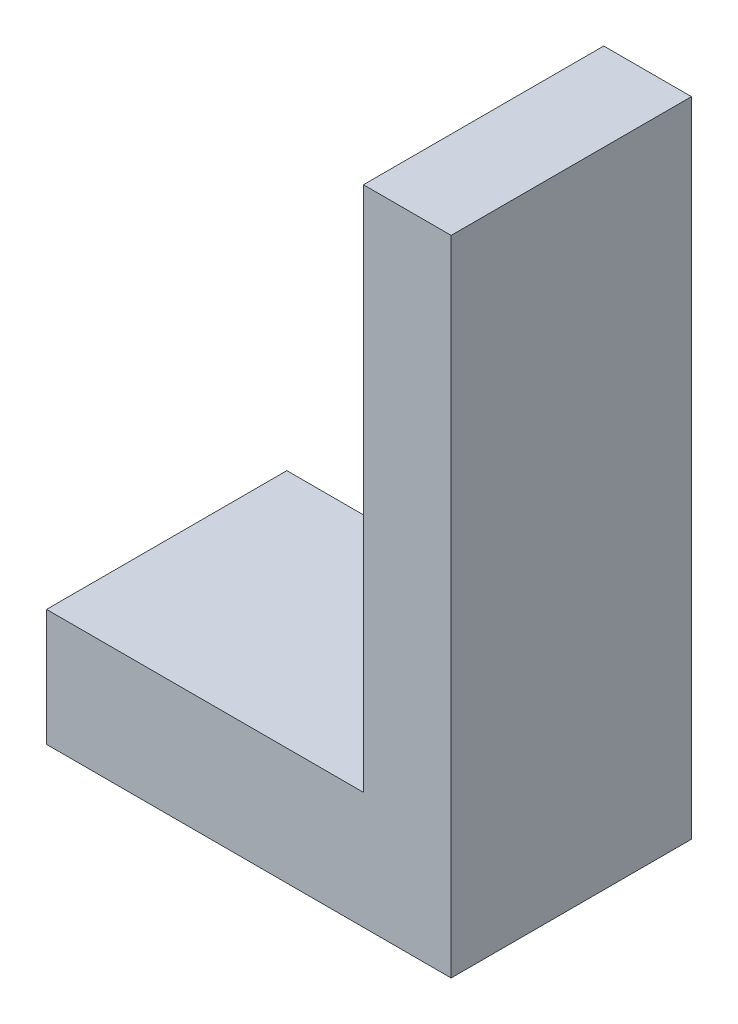
SolidWorks part; units mm, degrees
ref_plane "Front Plane" through (0, 0, 0) normal (0, 0, 1) x (1, 0, 0)
ref_plane "Top Plane" through (0, 0, 0) normal (0, 1, 0) x (1, 0, 0)
ref_plane "Right Plane" through (0, 0, 0) normal (1, 0, 0) x (0, 0, -1)
sketch "Sketch4" plane through (0, 0, 0) normal (0, 1, 0) x (1, 0, 0)
  line L1 (-34.6, -22.9) -> (34.6, -22.9)
  line L2 (-34.6, -22.9) -> (-34.6, 22.9)
  line L3 (-34.6, 22.9) -> (34.6, 22.9)
  line L4 (34.6, -22.9) -> (34.6, 22.9)
  line L5 (-34.6, -22.9) -> (34.6, 22.9) construction
  line L6 (-34.6, 22.9) -> (34.6, -22.9) construction
  line L7 (-15, -15) -> (15, -15)
  line L8 (-15, -15) -> (-15, 15)
  line L9 (-15, 15) -> (15, 15)
  line L10 (15, -15) -> (15, 15)
  line L11 (-15, -15) -> (15, 15) construction
  line L12 (-15, 15) -> (15, -15) construction
  point P0 (0, 0)
  point P6 (0, 0)
  dimension "D1" = 69.2
  dimension "D2" = 45.8
  dimension "D3" = 30
  dimension "D4" = 30
extrude "Boss-Extrude11" add sketch "Sketch4" along normal blind 10
sketch "Sketch9" plane through (0, 10, 0) normal (0, 1, 0) x (1, 0, 0)
  line L1 (-34.6, 22.9) -> (34.6, 22.9)
  line L2 (-34.6, 22.9) -> (-34.6, -22.9)
  line L3 (-34.6, -22.9) -> (34.6, -22.9)
  line L4 (34.6, 22.9) -> (34.6, -22.9)
extrude "Boss-Extrude12" add sketch "Sketch9" along normal blind 10
sketch "Sketch10" plane through (0, 20, 0) normal (0, 1, 0) x (1, 0, 0)
  line L0 (34.6, 22.9) -> (-34.6, 22.9) construction
  line L1 (34.6, -22.9) -> (19.6, -22.9)
  line L2 (34.6, -22.9) -> (34.6, 22.9)
  line L3 (34.6, 22.9) -> (19.6, 22.9)
  line L4 (19.6, -22.9) -> (19.6, 22.9)
  dimension "D1" = 15
extrude "Boss-Extrude13" add sketch "Sketch10" along normal blind 100
other "Move Face2" face at (6.5333, 46.6667, -22.9) parameters "D1"=4.7
other "Move Face3" face at (0, 10, 0) parameters "D1"=10
sketch "Sketch11" plane through (0, 0, 0) normal (0, -1, 0) x (1, 0, 0)
  line L5 (7.51, -5.15) -> (-17.49, -5.15)
  line L6 (7.51, -5.15) -> (7.51, 19.85)
  line L7 (7.51, 19.85) -> (-17.49, 19.85)
  line L8 (-17.49, -5.15) -> (-17.49, 19.85)
extrude "Cut-Extrude1" cut sketch "Sketch11" against normal blind 10
other "Move Face4" face at (27.1, 120, 2.35) parameters "D1"=10
